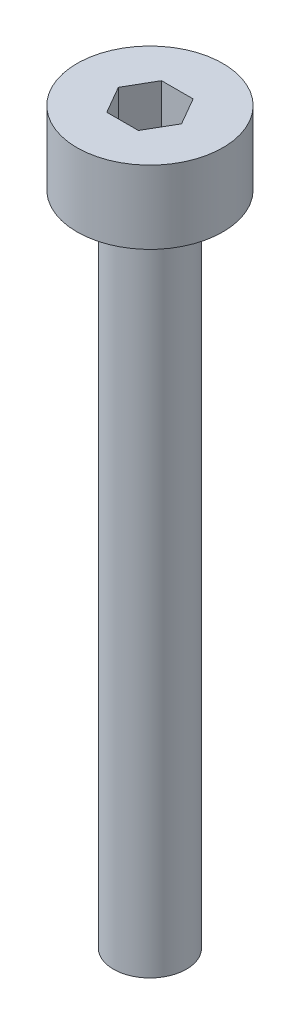
SolidWorks part; units mm, degrees
material "AISI 304"
ref_plane "前视基准面" through (0, 0, 0) normal (0, 0, 1) x (1, 0, 0)
ref_plane "上视基准面" through (0, 0, 0) normal (0, 1, 0) x (1, 0, 0)
ref_plane "右视基准面" through (0, 0, 0) normal (1, 0, 0) x (0, 0, -1)
sketch "草图1" plane through (0, 0, 0) normal (0, 1, 0) x (1, 0, 0)
  circle A0 centre (0, 0) radius 2
  dimension "D1" = 4
extrude "杯头高度" add sketch "草图1" along normal blind 2
sketch "草图2" plane through (0, 2, 0) normal (0, 1, 0) x (1, 0, 0)
  line L1 (0.866, 0) -> (0.433, 0.75)
  line L2 (0.433, 0.75) -> (-0.433, 0.75)
  line L3 (-0.433, 0.75) -> (-0.866, 0)
  line L4 (-0.866, 0) -> (-0.433, -0.75)
  line L5 (-0.433, -0.75) -> (0.433, -0.75)
  line L6 (0.433, -0.75) -> (0.866, 0)
  circle A0 centre (0, 0) radius 0.75 construction
  dimension "D1" = 1.5
extrude "内六角深度" cut sketch "草图2" against normal blind 1.5
sketch "草图3" plane through (0, 0, 0) normal (0, -1, 0) x (1, 0, 0)
  circle A0 centre (0, 0) radius 1
  dimension "D1" = 2
extrude "螺纹长度" add sketch "草图3" along normal blind 18
